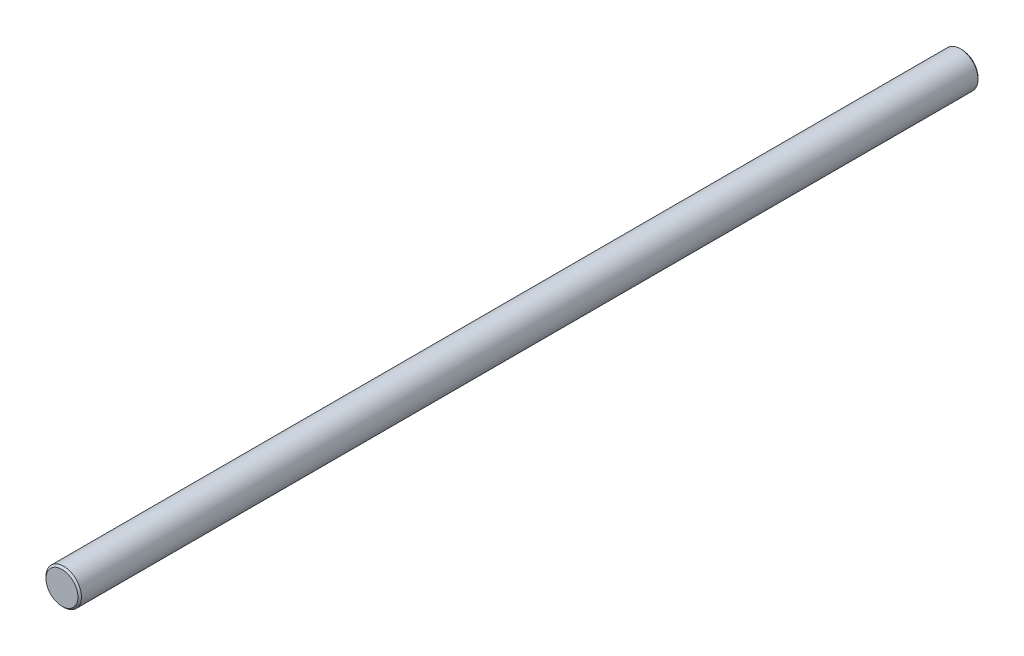
SolidWorks part; units mm, degrees
ref_plane "Front Plane" through (0, 0, 0) normal (0, 0, 1) x (1, 0, 0)
ref_plane "Top Plane" through (0, 0, 0) normal (0, 1, 0) x (1, 0, 0)
ref_plane "Right Plane" through (0, 0, 0) normal (1, 0, 0) x (0, 0, -1)
sketch "Sketch1" plane through (0, 0, 0) normal (0, 0, 1) x (1, 0, 0)
  circle A0 centre (0, 0) radius 10
  dimension "D1" = 20
extrude "Boss-Extrude1" add sketch "Sketch1" along normal blind 507
chamfer "Chamfer1" distance 1 angle 45 2 edges at (10, 0, 0) (10, 0, 507)
